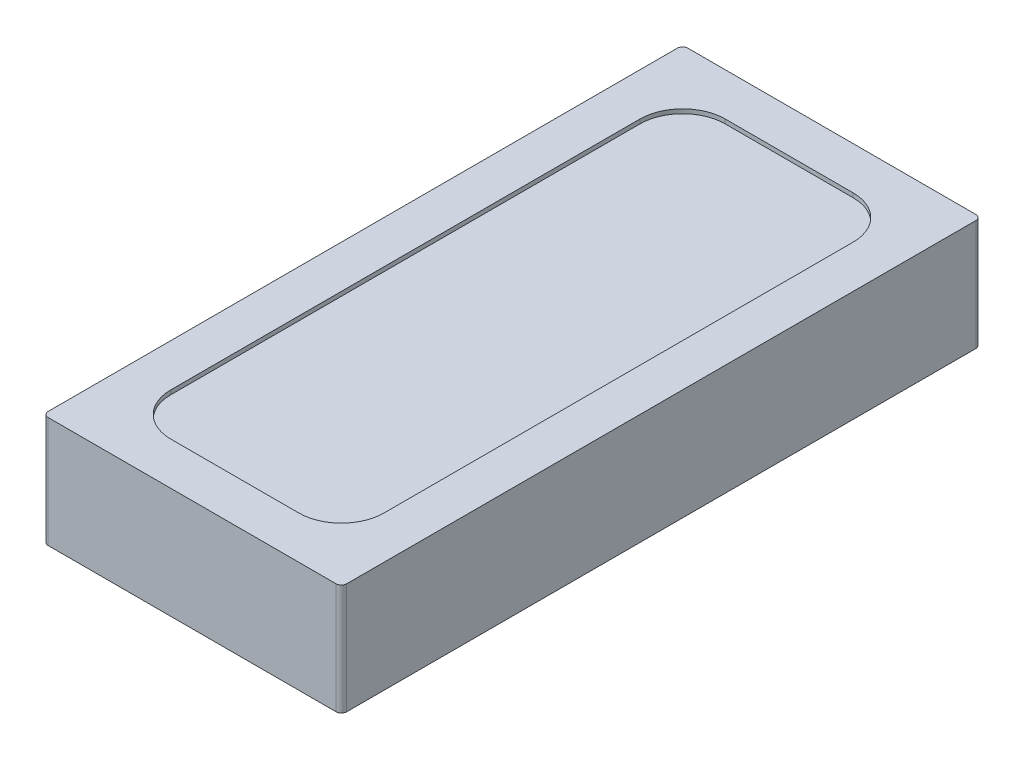
SolidWorks part; units mm, degrees
ref_plane "Front Plane" through (0, 0, 0) normal (0, 0, 1) x (1, 0, 0)
ref_plane "Top Plane" through (0, 0, 0) normal (0, 1, 0) x (1, 0, 0)
ref_plane "Right Plane" through (0, 0, 0) normal (1, 0, 0) x (0, 0, -1)
sketch "Sketch1" plane through (0, 0, 0) normal (0, 1, 0) x (1, 0, 0)
  line L1 (-0.675, -1.5) -> (0.675, -1.5)
  line L2 (-0.7, -1.475) -> (-0.7, 1.475)
  line L3 (-0.675, 1.5) -> (0.675, 1.5)
  line L4 (0.7, -1.475) -> (0.7, 1.475)
  line L5 (-0.7, -1.5) -> (0.7, 1.5) construction
  line L6 (-0.7, 1.5) -> (0.7, -1.5) construction
  arc A0 (-0.7, 1.475) -> (-0.675, 1.5) centre (-0.675, 1.475) cw
  arc A1 (0.675, 1.5) -> (0.7, 1.475) centre (0.675, 1.475) cw
  arc A2 (0.675, -1.5) -> (0.7, -1.475) centre (0.675, -1.475) ccw
  arc A3 (-0.675, -1.5) -> (-0.7, -1.475) centre (-0.675, -1.475) cw
  point P0 (0, 0)
  dimension "D3" = 0.025
  dimension "D1" = 1.4
  dimension "D2" = 3
extrude "Boss-Extrude1" add sketch "Sketch1" along normal blind 0.52
sketch "Sketch2" plane through (0, 0.52, 0) normal (0, 1, 0) x (1, 0, 0)
  line L1 (-0.3, -1.3) -> (0.3, -1.3)
  line L2 (-0.5, -1.1) -> (-0.5, 1.1)
  line L3 (-0.3, 1.3) -> (0.3, 1.3)
  line L4 (0.5, -1.1) -> (0.5, 1.1)
  line L5 (-0.5, -1.3) -> (0.5, 1.3) construction
  line L6 (-0.5, 1.3) -> (0.5, -1.3) construction
  arc A0 (0.3, -1.3) -> (0.5, -1.1) centre (0.3, -1.1) ccw
  arc A1 (0.3, 1.3) -> (0.5, 1.1) centre (0.3, 1.1) cw
  arc A2 (-0.5, 1.1) -> (-0.3, 1.3) centre (-0.3, 1.1) cw
  arc A3 (-0.3, -1.3) -> (-0.5, -1.1) centre (-0.3, -1.1) cw
  point P0 (0, 0)
  dimension "D3" = 0.2
  dimension "D1" = 2.6
  dimension "D2" = 1
extrude "Cut-Extrude1" cut sketch "Sketch2" against normal blind 0.02
sketch "Sketch3" plane through (0, 0.52, 0) normal (0, 1, 0) x (1, 0, 0)
  line L0 (-0.6927, -1.4927) -> (0, -0.8) construction
  line L1 (0, -0.8) -> (0.6927, -1.4927) construction
  line L2 (0.7, 0) -> (-0.7, 0) construction
  line L3 (0.7, -1.475) -> (0.7, 1.475) construction
  line L4 (-0.7, 1.475) -> (-0.7, -1.475) construction
  line L5 (-0.6927, 1.4927) -> (0, 0.8) construction
  line L6 (0, 0.8) -> (0.6927, 1.4927) construction
  arc A0 (-0.7, -1.475) -> (-0.675, -1.5) centre (-0.675, -1.475) ccw construction
  arc A1 (0.675, -1.5) -> (0.7, -1.475) centre (0.675, -1.475) ccw construction
sketch "Sketch4" plane through (0, 0, 0) normal (0, -1, 0) x (1, 0, 0)
  line L0 (0, -0.8) -> (0.6927, -1.4927) construction
  line L1 (-0.6927, -1.4927) -> (0, -0.8) construction
  line L2 (0, -0.8) -> (0.6927, -1.4927)
  line L3 (-0.6927, -1.4927) -> (0, -0.8)
  line L4 (0, 0.8) -> (0.6927, 1.4927) construction
  line L5 (-0.6927, 1.4927) -> (0, 0.8) construction
  line L6 (0, 0.8) -> (0.6927, 1.4927)
  line L7 (-0.6927, 1.4927) -> (0, 0.8)
  dimension "D1" = 1.6
